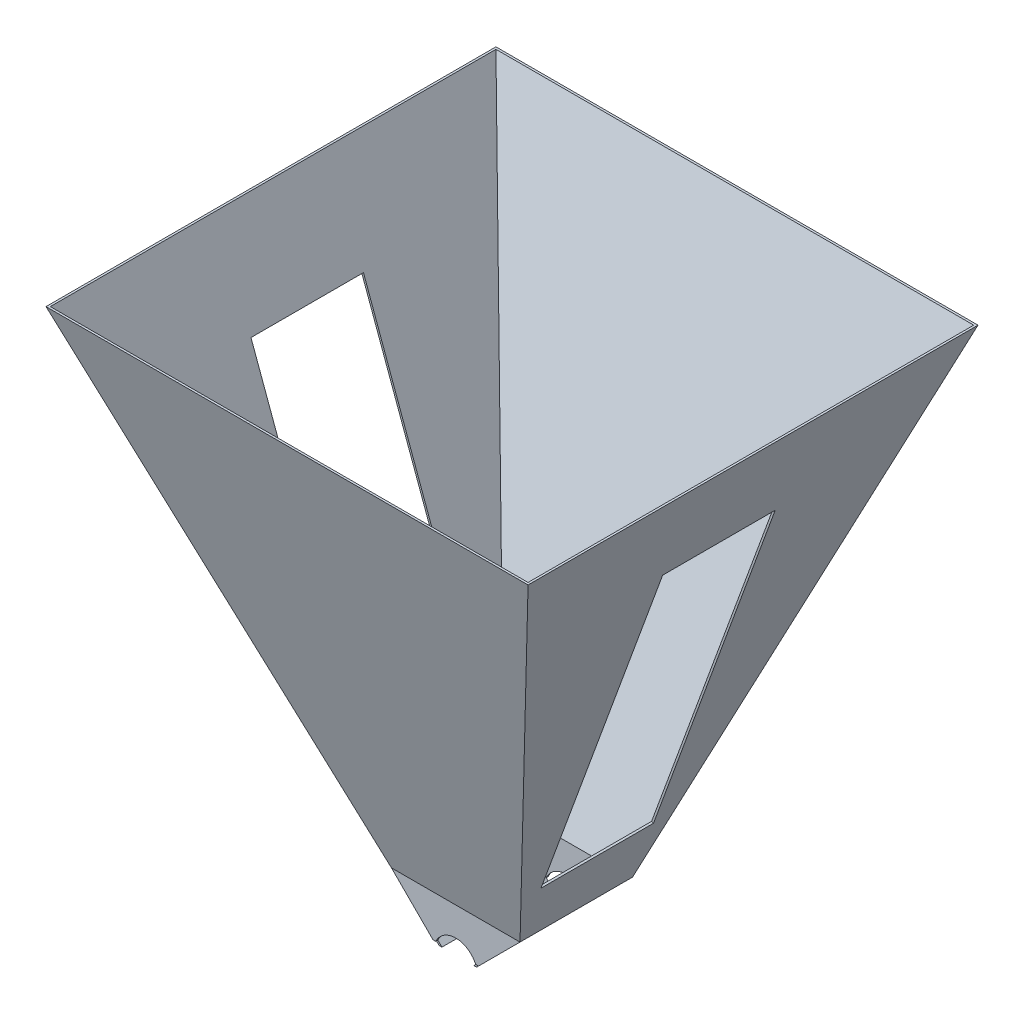
SolidWorks part; units mm, degrees
ref_plane "Front Plane" through (0, 0, 0) normal (0, 0, 1) x (1, 0, 0)
ref_plane "Top Plane" through (0, 0, 0) normal (0, 1, 0) x (1, 0, 0)
ref_plane "Right Plane" through (0, 0, 0) normal (1, 0, 0) x (0, 0, -1)
sketch "Sketch1" plane through (0, 0, 0) normal (0, 0, 1) x (1, 0, 0)
  line L0 (-12.7, 0) -> (12.7, 0)
  line L1 (12.7, 0) -> (50.8, 38.1)
  line L2 (50.8, 38.1) -> (-50.8, 38.1)
  line L3 (-50.8, 38.1) -> (-12.7, 0)
  dimension "D1" = 135
  dimension "D2" = 135
  dimension "D3" = 25.4
  dimension "D4" = 38.1
extrude "Boss-Extrude1" add sketch "Sketch1" against normal blind 1.5875
sketch "Sketch2" plane through (0, 0, -1.5875) normal (0, 0, -1) x (-1, 0, 0)
  line L0 (12.7, 0) -> (50.8, 38.1)
  line L1 (50.8, 38.1) -> (48.5549, 38.1)
  line L2 (-50.8, 38.1) -> (50.8, 38.1) construction
  line L3 (48.5549, 38.1) -> (10.4549, 0)
  line L4 (12.7, 0) -> (-12.7, 0) construction
  line L5 (10.4549, 0) -> (12.7, 0)
  line L6 (-48.5549, 38.1) -> (-10.4549, 0)
  line L7 (-10.4549, 0) -> (-12.7, 0)
  line L8 (-12.7, 0) -> (-50.8, 38.1) construction
  line L9 (-48.5549, 38.1) -> (-50.8, 38.1)
  line L10 (-50.8, 38.1) -> (-12.7, 0)
  dimension "D1" = 1.5875
  dimension "D2" = 1.5875
extrude "Boss-Extrude2" add sketch "Sketch2" along normal blind 85.725
sketch "Sketch3" plane through (0, 0, -87.3125) normal (0, 0, -1) x (-1, 0, 0)
  line L0 (-50.8, 38.1) -> (-12.7, 0)
  line L1 (-12.7, 0) -> (12.7, 0)
  line L2 (12.7, 0) -> (50.8, 38.1)
  line L3 (50.8, 38.1) -> (-50.8, 38.1)
extrude "Boss-Extrude3" add sketch "Sketch3" along normal blind 1.5875
sketch "Sketch9" plane through (0, 0, 0) normal (0, 0, 1) x (1, 0, 0)
  line L0 (-48.5549, 38.1) -> (-10.4549, 0) construction
  line L1 (10.4549, 0) -> (48.5549, 38.1) construction
  line L2 (-15.7551, 5.3001) -> (-10.4549, 0)
  line L3 (-10.4549, 0) -> (10.4549, 0)
  line L4 (10.4549, 0) -> (15.7551, 5.3001)
  arc A0 (-15.7551, 5.3001) -> (15.7551, 5.3001) centre (0, -1.778) cw
  point P3 (0, 15.494)
  point P9 (0, 0)
  dimension "D1" = 17.272
  dimension "D2" = 15.494
extrude "Cut-Extrude3" cut sketch "Sketch9" against normal through all both and the other way through all contours A0 L4 L3 L2
sketch "Sketch10" plane through (0, 0, 0) normal (0, 0, 1) x (1, 0, 0)
  line L0 (-10.4549, 0) -> (-12.7, 0)
  line L1 (-10.4549, 0) -> (-15.7551, 5.3001)
  line L2 (-15.7551, 5.3001) -> (-18.0001, 5.3001)
  line L3 (-50.8, 38.1) -> (-12.7, 0) construction
  line L4 (-18.0001, 5.3001) -> (-12.7, 0)
  line L5 (10.4549, 0) -> (12.7, 0)
  line L6 (10.4549, 0) -> (15.7551, 5.3001)
  line L7 (15.7551, 5.3001) -> (18.0001, 5.3001)
  line L8 (12.7, 0) -> (50.8, 38.1) construction
  line L9 (18.0001, 5.3001) -> (12.7, 0)
extrude "Cut-Extrude4" cut sketch "Sketch10" against normal blind 1.651
sketch "Sketch12" plane through (0, 0, -88.9) normal (0, 0, -1) x (-1, 0, 0)
  line L4 (10.4549, 0) -> (12.7, 0)
  line L5 (12.7, 0) -> (18.0001, 5.3001)
  line L6 (18.0001, 5.3001) -> (15.7551, 5.3001)
  line L7 (15.7551, 5.3001) -> (10.4549, 0)
  line L8 (10.4549, 0) -> (12.7, 0)
  line L9 (12.7, 0) -> (18.0001, 5.3001)
  line L10 (18.0001, 5.3001) -> (15.7551, 5.3001)
  line L11 (15.7551, 5.3001) -> (10.4549, 0)
  line L12 (-18.0001, 5.3001) -> (-12.7, 0)
  line L13 (-12.7, 0) -> (-10.4549, 0)
  line L14 (-10.4549, 0) -> (-15.7551, 5.3001)
  line L15 (-15.7551, 5.3001) -> (-18.0001, 5.3001)
  line L16 (-18.0001, 5.3001) -> (-12.7, 0)
  line L17 (-12.7, 0) -> (-10.4549, 0)
  line L18 (-10.4549, 0) -> (-15.7551, 5.3001)
  line L19 (-15.7551, 5.3001) -> (-18.0001, 5.3001)
  dimension "D1" = 0
  dimension "D2" = 0
extrude "Cut-Extrude5" cut sketch "Sketch12" against normal blind 1.651
sketch "Sketch13" plane through (0, 0, -1.651) normal (0, 0, 1) x (1, 0, 0)
  line L0 (-15.7551, 5.3001) -> (-18.0001, 5.3001) construction
  line L1 (-18.3825, 0) -> (18.5282, 0)
  line L2 (-18.3825, 0) -> (-18.3825, 2.1251)
  line L3 (-18.3825, 2.1251) -> (18.5282, 2.1251)
  line L4 (18.5282, 0) -> (18.5282, 2.1251)
  dimension "D1" = 3.175
extrude "Cut-Extrude6" cut sketch "Sketch13" against normal through all both and the other way through all
ref_plane "Plane1" through (0, 419.1, 0) normal (0, 1, 0) x (1, 0, 0)
sketch "Sketch4" plane through (0, 419.1, 0) normal (0, 1, 0) x (1, 0, 0)
  line L1 (-190.5, -133.35) -> (190.5, -133.35)
  line L2 (-190.5, -133.35) -> (-190.5, 222.25)
  line L3 (-190.5, 222.25) -> (190.5, 222.25)
  line L4 (190.5, -133.35) -> (190.5, 222.25)
  dimension "D1" = 381
  dimension "D2" = 355.6
  dimension "D3" = 190.5
sketch "Sketch5" plane through (0, 38.1, 0) normal (0, 1, 0) x (1, 0, 0)
  line L0 (-48.5549, 87.3125) -> (-48.5549, 1.5875) construction
  line L1 (-50.8, 88.9) -> (-50.8, 0) construction
  line L2 (-48.5549, 87.3125) -> (48.5549, 87.3125) construction
  line L3 (-50.8, 88.9) -> (50.8, 88.9) construction
  line L4 (48.5549, 87.3125) -> (48.5549, 1.5875) construction
  line L5 (50.8, 88.9) -> (50.8, 0) construction
  line L6 (50.8, 0) -> (-50.8, 0) construction
  line L7 (48.5549, 1.5875) -> (-48.5549, 1.5875) construction
  line L8 (-48.5549, 87.3125) -> (-48.5549, 1.5875)
  line L9 (-50.8, 88.9) -> (-50.8, 0)
  line L10 (-48.5549, 87.3125) -> (48.5549, 87.3125)
  line L11 (-50.8, 88.9) -> (50.8, 88.9)
  line L12 (48.5549, 87.3125) -> (48.5549, 1.5875)
  line L13 (50.8, 88.9) -> (50.8, 0)
  line L14 (50.8, 0) -> (-50.8, 0)
  line L15 (48.5549, 1.5875) -> (-48.5549, 1.5875)
loft "Loft1" add section "Sketch5" section "Sketch4"
shell "Shell1" thickness 1.5875
sketch "Sketch6" plane through (32.4652, -11.9039, 0) normal (0.9389, -0.3443, 0) x (0, 0, -1)
  line L1 (-0.0377, 101.4063) -> (88.9, 101.4063)
  line L2 (-0.0377, 101.4063) -> (-0.0377, 380.8063)
  line L3 (-0.0377, 380.8063) -> (88.9, 380.8063)
  line L4 (88.9, 101.4063) -> (88.9, 380.8063)
  dimension "D1" = 279.4
extrude "Cut-Extrude1" cut sketch "Sketch6" against normal blind 2.54
sketch "Sketch8" plane through (-32.4652, -11.9039, 0) normal (-0.9389, -0.3443, 0) x (0, 0, 1)
  line L1 (-88.9, 100.752) -> (0, 100.752)
  line L2 (-88.9, 100.752) -> (-88.9, 380.152)
  line L3 (-88.9, 380.152) -> (0, 380.152)
  line L4 (0, 100.752) -> (0, 380.152)
  dimension "D1" = 279.4
extrude "Cut-Extrude2" cut sketch "Sketch8" against normal blind 2.54
